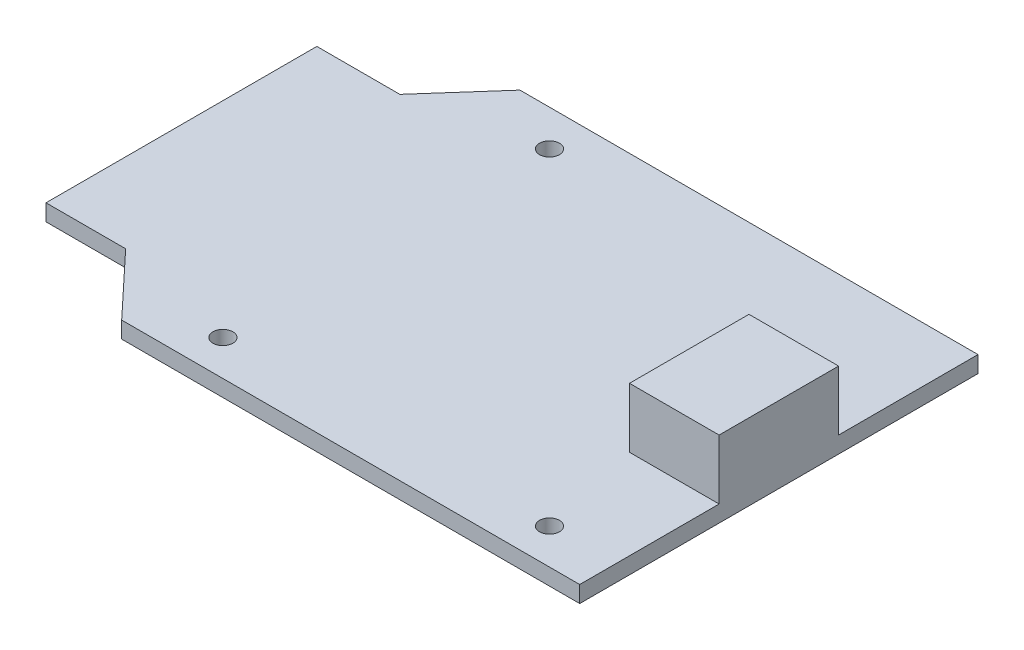
SolidWorks part; units mm, degrees
ref_plane "Front Plane" through (0, 0, 0) normal (0, 0, 1) x (1, 0, 0)
ref_plane "Top Plane" through (0, 0, 0) normal (0, 1, 0) x (1, 0, 0)
ref_plane "Right Plane" through (0, 0, 0) normal (1, 0, 0) x (0, 0, -1)
sketch "Sketch1" plane through (0, 0, 0) normal (0, 1, 0) x (1, 0, 0)
  line L0 (0, 0) -> (-2.83, -3.2)
  line L1 (0, 0) -> (23, 0)
  line L3 (0, -20) -> (23, -20)
  line L4 (23, 0) -> (23, -20)
  line L5 (-7, -3.2) -> (-2.83, -3.2)
  line L6 (-7, -3.2) -> (-7, -16.8)
  line L7 (-7, -16.8) -> (-3, -16.8)
  line L9 (0, -20) -> (-3, -16.8)
  circle A0 centre (3.3, -18.2173) radius 0.5
  circle A1 centre (3.3, -1.8173) radius 0.5
  circle A2 centre (19.7, -18.2173) radius 0.5
  dimension "D6" = 16.4
  dimension "D1" = 23
  dimension "D2" = 20
  dimension "D3" = 4.17
  dimension "D4" = 13.6
  dimension "D5" = 30
  dimension "D7" = 0
  dimension "D8" = 16.4
  dimension "D9" = 0
  dimension "D10" = 3.3
extrude "Boss-Extrude1" add sketch "Sketch1" along normal blind 0.83
ref_plane "Plane1" through (0, 0.83, 0) normal (0, 1, 0) x (1, 0, 0)
sketch "Sketch2" plane through (0, 0.83, 0) normal (0, 1, 0) x (1, 0, 0)
  line L0 (23, -20) -> (23, 0) construction
  line L1 (23, -7) -> (18.5, -7)
  line L2 (23, -7) -> (23, -13)
  line L3 (23, -13) -> (18.5, -13)
  line L4 (18.5, -7) -> (18.5, -13)
  dimension "D1" = 6
  dimension "D2" = 4.5
  dimension "D3" = 7
  dimension "D4" = 7
extrude "Boss-Extrude2" add sketch "Sketch2" along normal blind 3
